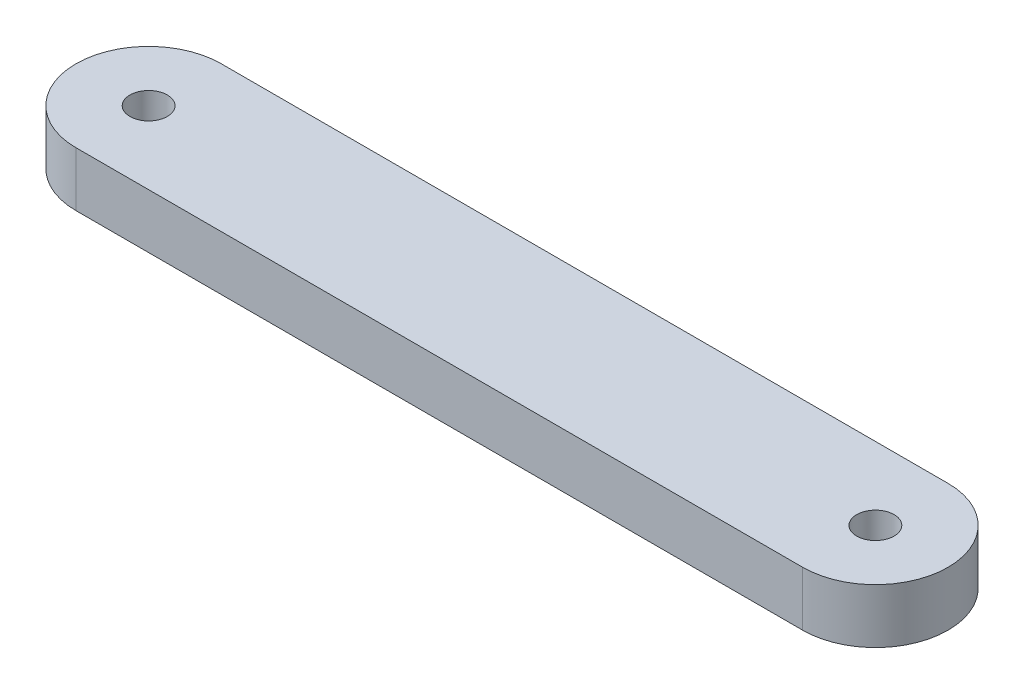
SolidWorks part; units mm, degrees
material "6061-T6 (SS)"
ref_plane "Front Plane" through (0, 0, 0) normal (0, 0, 1) x (1, 0, 0)
ref_plane "Top Plane" through (0, 0, 0) normal (0, 1, 0) x (1, 0, 0)
ref_plane "Right Plane" through (0, 0, 0) normal (1, 0, 0) x (0, 0, -1)
sketch "Sketch1" plane through (0, 0, 0) normal (0, 1, 0) x (1, 0, 0)
  line L0 (-63.5, 0) -> (0, 0) construction
  line L1 (-63.5, 6.35) -> (0, 6.35)
  line L2 (-63.5, -6.35) -> (0, -6.35)
  arc A0 (-63.5, 6.35) -> (-63.5, -6.35) centre (-63.5, 0) ccw
  arc A1 (0, -6.35) -> (0, 6.35) centre (0, 0) ccw
  point P2 (-31.75, 0)
  point P9 (-69.85, 0)
  point P10 (6.35, 0)
  dimension "D2" = 76.2
  dimension "D1" = 12.7
extrude "Boss-Extrude2" add sketch "Sketch1" along normal blind 4.7625
hole_wizard "#4 Clearance Hole1" positions "Sketch2" profile "Sketch4" hole size "#4" standard "ANSI Inch" end condition through all
sketch "Sketch2" plane through (0, 4.7625, 0) normal (0, 1, 0) x (1, 0, 0)
  point P3 (-63.5, 0)
  point P8 (0, 0)
sketch "Sketch4" plane through (-63.5, 4.7625, 0) normal (1, 0, 0) x (0, 0, 1)
  line L0 (0, 0) -> (0, 4.7625)
  line L1 (0, 4.7625) -> (1.6319, 4.7625)
  line L2 (1.6319, 4.7625) -> (1.6319, 0)
  line L5 (1.6319, 0) -> (0, 0)
  line L11 (0, -6.35) -> (0, 107.95) construction
  dimension "Thru Hole Dia." = 3.2639
  dimension "Thru Hole Depth" = 4.7625
hole_wizard "CSK for #4 Flat Head Socket Cap Screw2" positions "Sketch8" profile "Sketch9" countersink size "#4" standard "ANSI Inch" end condition through all
sketch "Sketch8" plane through (0, 0, 0) normal (0, -1, 0) x (-1, 0, 0)
  point P0 (0, 0)
sketch "Sketch9" plane through (0, 0, 0) normal (1, 0, 0) x (0, 0, -1)
  line L0 (0, 0) -> (0, 4.7625)
  line L1 (0, 4.7625) -> (1.6319, 4.7625)
  line L2 (1.6319, 4.7625) -> (1.6319, 1.8481)
  line L3 (1.6319, 1.8481) -> (3.2385, 0)
  line L5 (3.2385, 0) -> (0, 0)
  line L6 (-1.6319, 1.8481) -> (-3.2385, 0) construction
  line L11 (0, -6.35) -> (0, 107.95) construction
  dimension "Thru Hole Dia." = 3.2639
  dimension "Thru Hole Depth" = 4.7625
  dimension "Near C'Sink Dia." = 6.477
  dimension "Near C'Sink Angle" = 82
